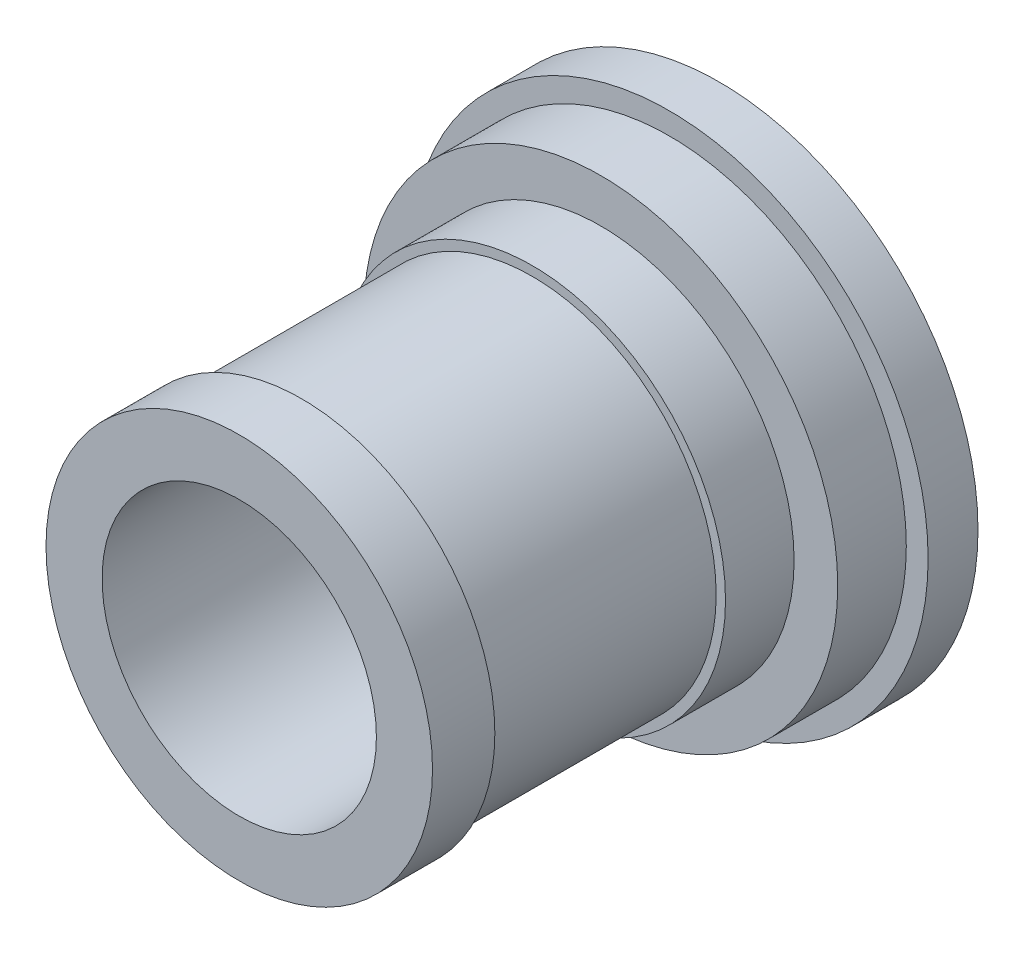
SolidWorks part; units mm, degrees
ref_plane "Front Plane" through (0, 0, 0) normal (0, 0, 1) x (1, 0, 0)
ref_plane "Top Plane" through (0, 0, 0) normal (0, 1, 0) x (1, 0, 0)
ref_plane "Right Plane" through (0, 0, 0) normal (1, 0, 0) x (0, 0, -1)
sketch "Sketch1" plane through (0, 0, 0) normal (0, 1, 0) x (1, 0, 0)
  line L0 (0, 0) -> (0, 85.4922) construction
  line L1 (22, 0) -> (31, 0)
  line L2 (31, 58) -> (31, 47)
  line L3 (31, 47) -> (29.5, 47)
  line L4 (29.5, 47) -> (29.5, 10)
  line L5 (29.5, 10) -> (31, 10)
  line L6 (31, 10) -> (31, 0)
  line L7 (31, 58) -> (38, 58)
  line L8 (38, 58) -> (38, 69)
  line L9 (38, 69) -> (41.5, 69)
  line L10 (41.5, 69) -> (41.5, 77)
  line L11 (41.5, 77) -> (22, 77)
  line L13 (22, 77) -> (22, 0)
  dimension "D1" = 10
  dimension "D2" = 37
  dimension "D3" = 11
  dimension "D4" = 11
  dimension "D5" = 8
  dimension "D6" = 83
  dimension "D7" = 76
  dimension "D8" = 62
  dimension "D9" = 59
  dimension "D10" = 62
  dimension "D11" = 44
revolve "Revolve1" add sketch "Sketch1" angle 360 about L0
